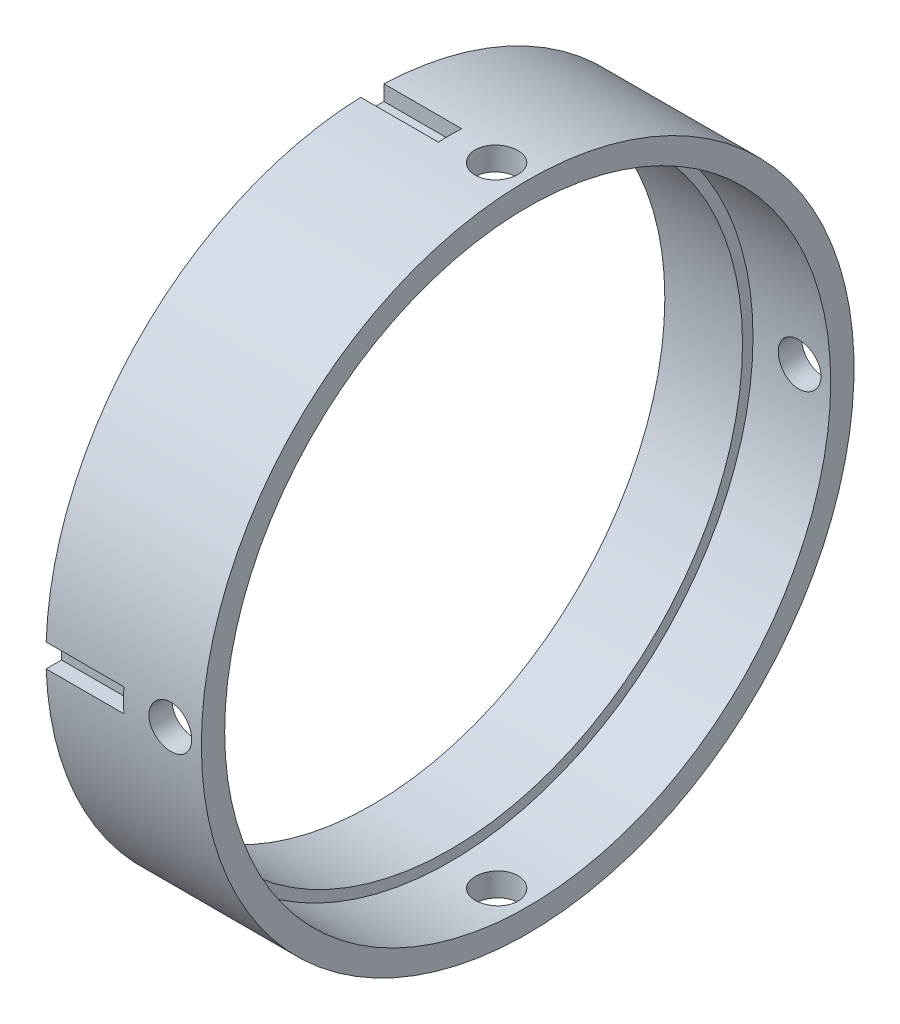
SolidWorks part; units mm, degrees
ref_plane "Plan de face" through (0, 0, 0) normal (0, 0, 1) x (1, 0, 0)
ref_plane "Plan de dessus" through (0, 0, 0) normal (0, 1, 0) x (1, 0, 0)
ref_plane "Plan de droite" through (0, 0, 0) normal (1, 0, 0) x (0, 0, -1)
sketch "Esquisse1" plane through (0, 0, 0) normal (0, 0, 1) x (1, 0, 0)
  line L0 (0, 37.65) -> (10, 37.65)
  line L1 (10, 37.65) -> (10, 39)
  line L2 (10, 39) -> (20, 39)
  line L3 (20, 39) -> (20, 42)
  line L4 (20, 42) -> (0, 42)
  line L5 (0, 42) -> (0, 37.65)
  line L6 (0, 0) -> (35.5501, 0) construction
  dimension "D1" = 42
  dimension "D2" = 10
  dimension "D3" = 3
  dimension "D4" = 4.35
  dimension "D5" = 20
revolve "Révolution1" add sketch "Esquisse1" angle 360 about L6
hole_wizard "Dégagement M51" positions "Esquisse3D2" profile "Esquisse4" hole size "M5" standard "ISO" end condition through all
sketch3d "Esquisse3D2"
  line L2 (0, 0, 0) -> (0, 126.2496, 0) construction
  line L4 (0, 42, 0) -> (37.1483, 42, 0) construction
  point P0 (16, 42, 0)
  dimension "D1" = 16
sketch "Esquisse4" plane through (16, 42, 0) normal (1, 0, 0) x (0, 0, 1)
  line L0 (0, 0) -> (0, 84)
  line L1 (0, 84) -> (2.75, 84)
  line L2 (2.75, 84) -> (2.75, 0)
  line L5 (2.75, 0) -> (0, 0)
  line L11 (0, -6.35) -> (0, 107.95) construction
  dimension "Diamètre du perçage jusqu'au prochain" = 5.5
  dimension "Profondeur du perçage jusqu'au prochain" = 84
pattern_circular "Répétition circulaire1" count 2 over 90 about axis through (20, 0, 0) along (-1, 0, 0) of "Dégagement M51"
sketch "Esquisse5" plane through (0, 0, 0) normal (-1, 0, 0) x (0, 0, 1)
  line L0 (0, 0) -> (0, 80) construction
  line L1 (-1.5, 55) -> (1.5, 55)
  line L2 (-1.5, 55) -> (-1.5, 40)
  line L3 (-1.5, 40) -> (1.5, 40)
  line L4 (1.5, 55) -> (1.5, 40)
  point P7 (0, 40)
  dimension "D1" = 3
  dimension "D2" = 15
  dimension "D3" = 40
extrude "Enlèv. mat.-Extru.1" cut sketch "Esquisse5" against normal blind 10
pattern_circular "Répétition circulaire2" count 4 over 360 about axis through (0, 0, 0) along (1, 0, 0) of "Enlèv. mat.-Extru.1"
